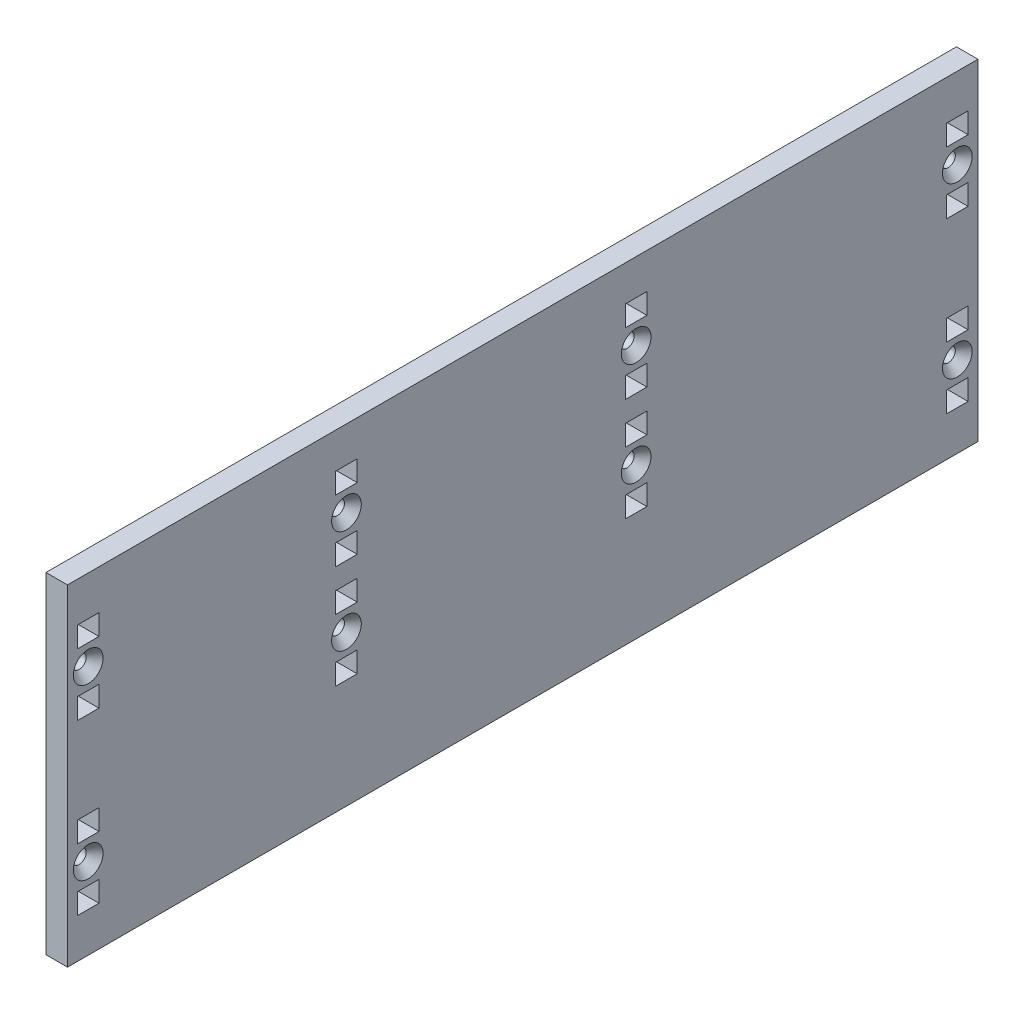
SolidWorks part; units mm, degrees
material "Acrylic (Blue)"
ref_plane "Front Plane" through (0, 0, 0) normal (0, 0, 1) x (1, 0, 0)
ref_plane "Top Plane" through (0, 0, 0) normal (0, 1, 0) x (1, 0, 0)
ref_plane "Right Plane" through (0, 0, 0) normal (1, 0, 0) x (0, 0, -1)
sketch "Sketch1" plane through (0, 0, 0) normal (1, 0, 0) x (0, 0, -1)
  line L0 (133.35, -24.8793) -> (133.35, -76.7207) construction
  line L1 (-139.7, 0) -> (139.7, 0)
  line L2 (-139.7, 0) -> (-139.7, -101.6)
  line L3 (-139.7, -101.6) -> (139.7, -101.6)
  line L4 (139.7, 0) -> (139.7, -101.6)
  line L5 (-133.35, -24.8793) -> (-133.35, -76.7207) construction
  line L6 (0, 0) -> (0, -101.6) construction
  line L7 (-133.35, -50.8) -> (0, -50.8) construction
  line L8 (0, -50.8) -> (133.35, -50.8) construction
  line B0 (-130.048, -31.2293) -> (-130.048, -37.5793)
  line B1 (-130.048, -37.5793) -> (-136.652, -37.5793)
  line B2 (-136.652, -37.5793) -> (-136.652, -31.2293)
  line B3 (-136.652, -31.2293) -> (-130.048, -31.2293)
  line B4 (-130.048, -12.1793) -> (-130.048, -18.5293)
  line B5 (-130.048, -18.5293) -> (-136.652, -18.5293)
  line B6 (-136.652, -18.5293) -> (-136.652, -12.1793)
  line B7 (-136.652, -12.1793) -> (-130.048, -12.1793)
  circle B8 centre (-133.35, -24.8793) radius 2.1526
  line B9 (-130.048, -83.0707) -> (-130.048, -89.4207)
  line B10 (-130.048, -89.4207) -> (-136.652, -89.4207)
  line B11 (-136.652, -89.4207) -> (-136.652, -83.0707)
  line B12 (-136.652, -83.0707) -> (-130.048, -83.0707)
  line B13 (-130.048, -64.0207) -> (-130.048, -70.3707)
  line B14 (-130.048, -70.3707) -> (-136.652, -70.3707)
  line B15 (-136.652, -70.3707) -> (-136.652, -64.0207)
  line B16 (-136.652, -64.0207) -> (-130.048, -64.0207)
  circle B17 centre (-133.35, -76.7207) radius 2.1526
  line B18 (130.048, -18.5293) -> (130.048, -12.1793)
  line B19 (130.048, -12.1793) -> (136.652, -12.1793)
  line B20 (136.652, -12.1793) -> (136.652, -18.5293)
  line B21 (136.652, -18.5293) -> (130.048, -18.5293)
  line B22 (130.048, -37.5793) -> (130.048, -31.2293)
  line B23 (130.048, -31.2293) -> (136.652, -31.2293)
  line B24 (136.652, -31.2293) -> (136.652, -37.5793)
  line B25 (136.652, -37.5793) -> (130.048, -37.5793)
  circle B26 centre (133.35, -24.8793) radius 2.1526
  line B27 (130.048, -70.3707) -> (130.048, -64.0207)
  line B28 (130.048, -64.0207) -> (136.652, -64.0207)
  line B29 (136.652, -64.0207) -> (136.652, -70.3707)
  line B30 (136.652, -70.3707) -> (130.048, -70.3707)
  line B31 (130.048, -89.4207) -> (130.048, -83.0707)
  line B32 (130.048, -83.0707) -> (136.652, -83.0707)
  line B33 (136.652, -83.0707) -> (136.652, -89.4207)
  line B34 (136.652, -89.4207) -> (130.048, -89.4207)
  circle B35 centre (133.35, -76.7207) radius 2.1526
  dimension "D1" = 6.35
  dimension "D2" = 101.6
  dimension "D3" = 266.7
  dimension "D4" = 51.8414
sketch_block_instance "BOLT_HOLE-1"
sketch_block "BOLT_HOLE" parameters "D1"=4.3053, "D2"=6.35, "D3"=6.35, "D4"=6.604
sketch_block_instance "BOLT_HOLE-2"
sketch_block_instance "BOLT_HOLE-3"
sketch_block_instance "BOLT_HOLE-4"
extrude "Boss-Extrude1" add sketch "Sketch1" along normal blind 6.604
sketch "Sketch2" plane through (6.604, 0, 0) normal (1, 0, 0) x (0, 0, -1)
  line L0 (139.7, 0) -> (-139.7, 0) construction
  line L1 (139.7, -101.6) -> (139.7, 0) construction
  line B0 (-57.404, -17.272) -> (-57.404, -10.922)
  line B1 (-57.404, -10.922) -> (-50.8, -10.922)
  line B2 (-50.8, -10.922) -> (-50.8, -17.272)
  line B3 (-50.8, -17.272) -> (-57.404, -17.272)
  line B4 (-57.404, -36.322) -> (-57.404, -29.972)
  line B5 (-57.404, -29.972) -> (-50.8, -29.972)
  line B6 (-50.8, -29.972) -> (-50.8, -36.322)
  line B7 (-50.8, -36.322) -> (-57.404, -36.322)
  circle B8 centre (-54.102, -23.622) radius 2.1526
  line B9 (31.496, -49.022) -> (31.496, -42.672)
  line B10 (31.496, -42.672) -> (38.1, -42.672)
  line B11 (38.1, -42.672) -> (38.1, -49.022)
  line B12 (38.1, -49.022) -> (31.496, -49.022)
  line B13 (31.496, -68.072) -> (31.496, -61.722)
  line B14 (31.496, -61.722) -> (38.1, -61.722)
  line B15 (38.1, -61.722) -> (38.1, -68.072)
  line B16 (38.1, -68.072) -> (31.496, -68.072)
  circle B17 centre (34.798, -55.372) radius 2.1526
  line B18 (-57.404, -49.022) -> (-57.404, -42.672)
  line B19 (-57.404, -42.672) -> (-50.8, -42.672)
  line B20 (-50.8, -42.672) -> (-50.8, -49.022)
  line B21 (-50.8, -49.022) -> (-57.404, -49.022)
  line B22 (-57.404, -68.072) -> (-57.404, -61.722)
  line B23 (-57.404, -61.722) -> (-50.8, -61.722)
  line B24 (-50.8, -61.722) -> (-50.8, -68.072)
  line B25 (-50.8, -68.072) -> (-57.404, -68.072)
  circle B26 centre (-54.102, -55.372) radius 2.1526
  line B27 (31.496, -17.272) -> (31.496, -10.922)
  line B28 (31.496, -10.922) -> (38.1, -10.922)
  line B29 (38.1, -10.922) -> (38.1, -17.272)
  line B30 (38.1, -17.272) -> (31.496, -17.272)
  line B31 (31.496, -36.322) -> (31.496, -29.972)
  line B32 (31.496, -29.972) -> (38.1, -29.972)
  line B33 (38.1, -29.972) -> (38.1, -36.322)
  line B34 (38.1, -36.322) -> (31.496, -36.322)
  circle B35 centre (34.798, -23.622) radius 2.1526
  dimension "D1" = 19.05
  dimension "D2" = 88.9
  dimension "D3" = 10.922
  dimension "D4" = 101.6
sketch_block_instance "BOLT_HOLE-5"
sketch_block_instance "BOLT_HOLE-6"
sketch_block_instance "BOLT_HOLE-7"
sketch_block_instance "BOLT_HOLE-8"
extrude "Cut-Extrude1" cut sketch "Sketch2" along direction (1, 0, 0) on the side against the normal through all
hole_wizard "CSK for #8 Flat Head Socket Cap Screw1" positions "Sketch4" profile "Sketch3" countersink size "#8" standard "ANSI Inch" end condition through all
sketch "Sketch4" plane through (6.604, 0, 0) normal (1, 0, 0) x (0, 0, -1)
  point P0 (-133.35, -24.8793)
  point P3 (-133.35, -76.7207)
  point P6 (-54.102, -55.372)
  point P9 (-54.102, -23.622)
  point P12 (34.798, -23.622)
  point P15 (34.798, -55.372)
  point P18 (133.35, -76.7207)
  point P21 (133.35, -24.8793)
sketch "Sketch3" plane through (6.604, -24.8793, 133.35) normal (0, 1, 0) x (0, 0, -1)
  line L0 (0, 0) -> (0, 6.604)
  line L1 (0, 6.604) -> (2.1526, 6.604)
  line L2 (2.1526, 6.604) -> (2.1526, 2.7685)
  line L3 (2.1526, 2.7685) -> (4.5593, 0)
  line L5 (4.5593, 0) -> (0, 0)
  line L6 (-2.1526, 2.7685) -> (-4.5593, 0) construction
  line L11 (0, -6.35) -> (0, 107.95) construction
  dimension "Thru Hole Dia." = 4.3053
  dimension "Thru Hole Depth" = 6.604
  dimension "Near C'Sink Dia." = 9.1186
  dimension "Near C'Sink Angle" = 82
other "Move Face1" [suppressed] parameters "D1"=0.0508
